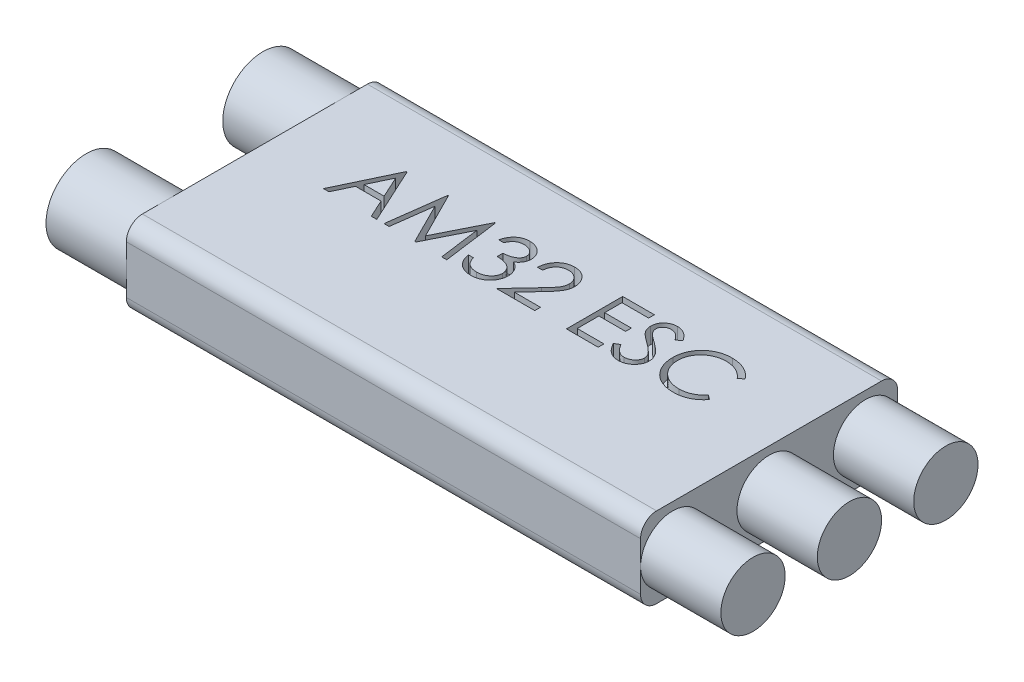
SolidWorks part; units mm, degrees
ref_plane "Front Plane" through (0, 0, 0) normal (0, 0, 1) x (1, 0, 0)
ref_plane "Top Plane" through (0, 0, 0) normal (0, 1, 0) x (1, 0, 0)
ref_plane "Right Plane" through (0, 0, 0) normal (1, 0, 0) x (0, 0, -1)
sketch "Sketch1" plane through (0, 0, 0) normal (0, 1, 0) x (1, 0, 0)
  line L1 (-16, -8) -> (16, -8)
  line L2 (-16, -8) -> (-16, 8)
  line L3 (-16, 8) -> (16, 8)
  line L4 (16, -8) -> (16, 8)
  line L5 (-16, -8) -> (16, 8) construction
  line L6 (-16, 8) -> (16, -8) construction
  point P0 (0, 0)
  dimension "D1" = 32
  dimension "D2" = 16
extrude "Boss-Extrude1" add sketch "Sketch1" along normal blind 5
sketch "Sketch2" plane through (0, 5, 0) normal (0, 1, 0) x (1, 0, 0)
  line L0 (-16, 0) -> (16, 0) construction
  line L1 (16, -8) -> (16, 8) construction
  text T0 "AM32 ESC"
  point P3 (1.2522, -2.704)
  point P6 (0, 0)
  point P8 (0, 0)
extrude "Cut-Extrude1" cut sketch "Sketch2" against normal blind 1
sketch "Sketch3" plane through (16, 0, 0) normal (1, 0, 0) x (0, 0, -1)
  line L0 (0, 0) -> (0, 5) construction
  line L1 (-8, 5) -> (8, 5) construction
  line L2 (0, 2.5) -> (-6, 2.5) construction
  line L3 (0, 2.5) -> (6, 2.5) construction
  line L4 (-8, 5) -> (-8, 0) construction
  circle A0 centre (-6, 2.5) radius 2
  circle A1 centre (0, 2.5) radius 2
  circle A2 centre (6, 2.5) radius 2
  dimension "D1" = 4
extrude "Boss-Extrude2" add sketch "Sketch3" along normal blind 5
sketch "Sketch4" plane through (-16, 0, 0) normal (-1, 0, 0) x (0, 0, 1)
  line L0 (0, 0) -> (0, 5) construction
  line L1 (-8, 0) -> (8, 0) construction
  line L2 (-8, 5) -> (8, 5) construction
  line L3 (0, 2.5) -> (-5.5, 2.5) construction
  line L4 (0, 2.5) -> (5.5, 2.5) construction
  line L5 (-8, 5) -> (-8, 0) construction
  circle A0 centre (-5.5, 2.5) radius 2.5
  circle A1 centre (5.5, 2.5) radius 2.5
extrude "Boss-Extrude3" add sketch "Sketch4" along normal blind 5
fillet "Fillet1" radius 1 4 edges at (0, 0, -8) (0, 5, -8) (0, 0, 8) (0, 5, 8)
